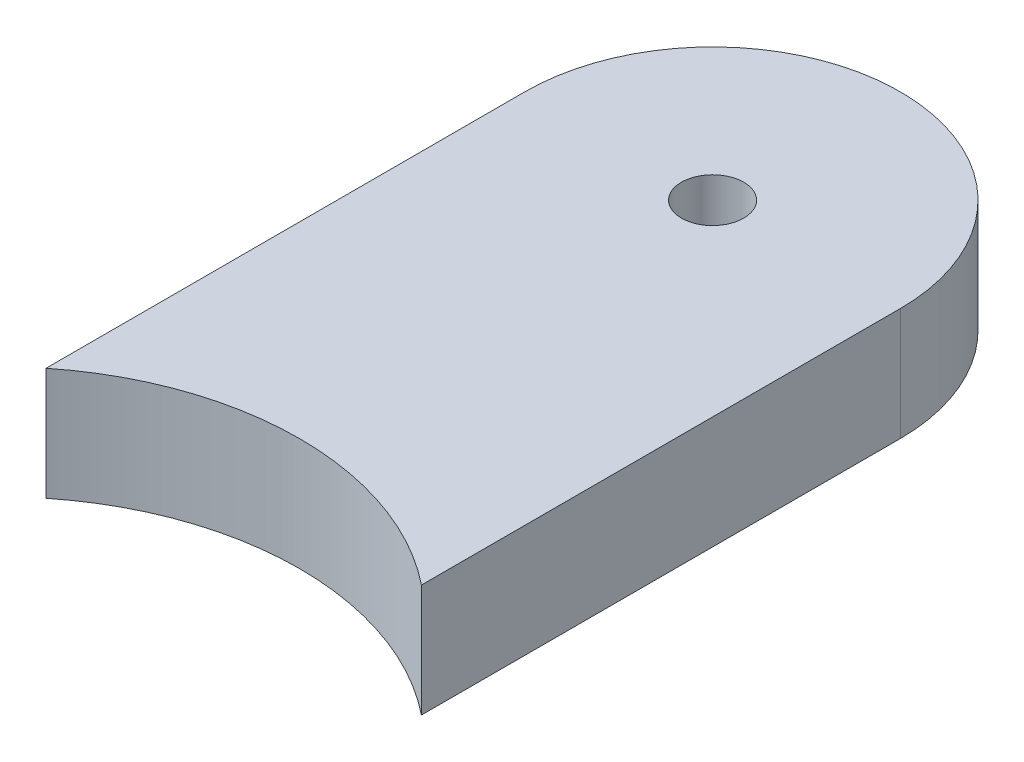
SolidWorks part; units mm, degrees
ref_plane "Plan de face" through (0, 0, 0) normal (0, 0, 1) x (1, 0, 0)
ref_plane "Plan de dessus" through (0, 0, 0) normal (0, 1, 0) x (1, 0, 0)
ref_plane "Plan de droite" through (0, 0, 0) normal (1, 0, 0) x (0, 0, -1)
sketch "Esquisse1" plane through (0, 0, 0) normal (0, 1, 0) x (1, 0, 0)
  line L0 (0, 0) -> (0, 223.7456) construction
  line L1 (25, 31.225) -> (25, 95)
  line L2 (-25, 31.225) -> (-25, 95)
  line L3 (25, 40) -> (-25, 40) construction
  line L4 (25, 120) -> (-25, 120) construction
  line L6 (25, 95) -> (-25, 95) construction
  line L9 (25, 0) -> (25, 223.7456) construction
  line L11 (-25, 0) -> (-25, 223.7456) construction
  arc A0 (25, 31.225) -> (-25, 31.225) centre (0, 0) ccw
  arc A1 (-25, 95) -> (25, 95) centre (0, 95) cw
  circle A2 centre (0, 95) radius 4.15
  dimension "D3" = 80
  dimension "D5" = 25
extrude "Boss.-Extru.1" add sketch "Esquisse1" along normal blind 15
